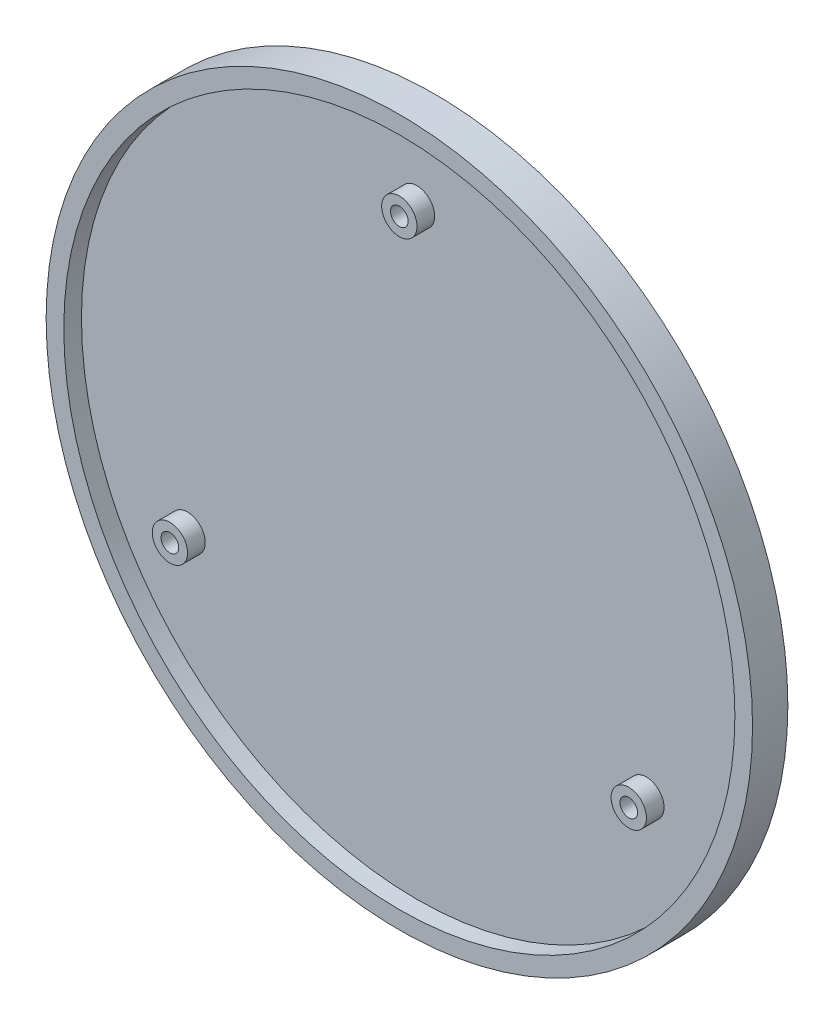
SolidWorks part; units mm, degrees
ref_plane "前视基准面" through (0, 0, 0) normal (0, 0, 1) x (1, 0, 0)
ref_plane "上视基准面" through (0, 0, 0) normal (0, 1, 0) x (1, 0, 0)
ref_plane "右视基准面" through (0, 0, 0) normal (1, 0, 0) x (0, 0, -1)
sketch "草图1" plane through (0, 0, 0) normal (0, 0, 1) x (1, 0, 0)
  circle A0 centre (0, 0) radius 40
extrude "凸台-拉伸1" add sketch "草图1" along normal blind 4
shell "抽壳1" thickness 2
sketch "草图2" plane through (0, 0, 2) normal (0, 0, 1) x (1, 0, 0)
  circle A1 centre (0, 30) radius 1
  circle A2 centre (0, 30) radius 2
  circle A3 centre (25.9808, -15) radius 2
  circle A4 centre (25.9808, -15) radius 1
  circle A5 centre (-25.9808, -15) radius 2
  circle A6 centre (-25.9808, -15) radius 1
  point P14 (0, 0)
  dimension "D1" = 3
extrude "凸台-拉伸2" add sketch "草图2" along normal blind 2
sketch "草图3" plane through (0, 0, 4) normal (0, 0, 1) x (1, 0, 0)
  circle A0 centre (25.9808, -15) radius 1
  circle A1 centre (-25.9808, -15) radius 1
  circle A2 centre (0, 30) radius 1
extrude "切除-拉伸1" cut sketch "草图3" against normal blind 20
sketch "草图4" plane through (0, 0, 0) normal (0, 0, -1) x (-1, 0, 0)
  circle A0 centre (-25.9808, -15) radius 1.6
  circle A1 centre (0, 30) radius 1.6
  circle A2 centre (25.9808, -15) radius 1.6
extrude "切除-拉伸2" cut sketch "草图4" against normal blind 1.2
